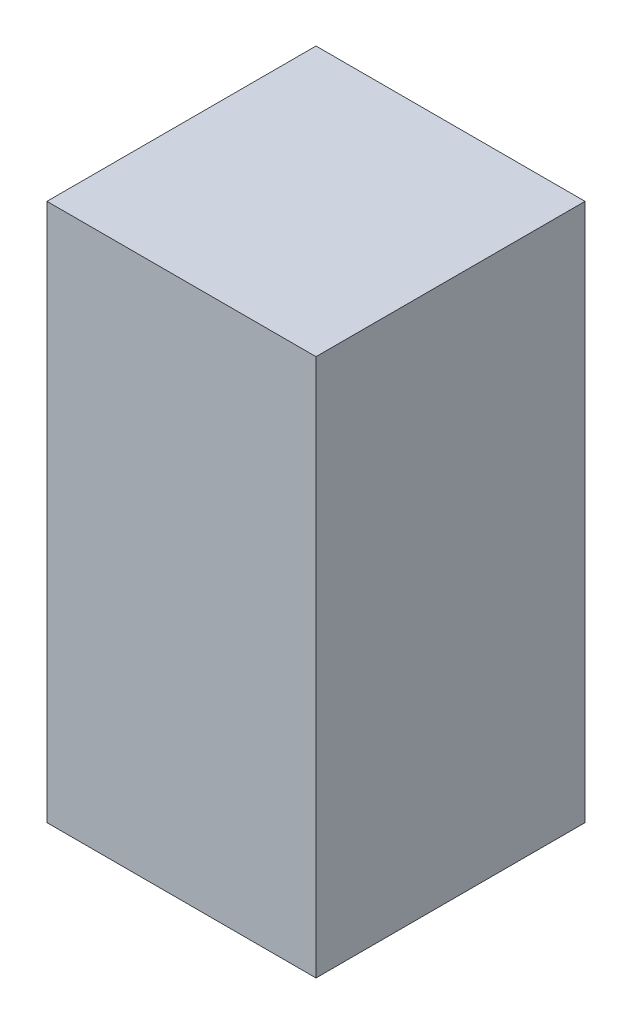
SolidWorks part; units mm, degrees
ref_plane "Front" through (0, 0, 0) normal (0, 0, 1) x (1, 0, 0)
ref_plane "Top" through (0, 0, 0) normal (0, 1, 0) x (1, 0, 0)
ref_plane "Right" through (0, 0, 0) normal (1, 0, 0) x (0, 0, -1)
sketch "Sketch1" plane through (0, 0, 0) normal (0, 1, 0) x (1, 0, 0)
  line L1 (0, 0) -> (200, 0)
  line L2 (0, 0) -> (0, -200)
  line L3 (0, -200) -> (200, -200)
  line L4 (200, 0) -> (200, -200)
  dimension "D1" = 200
  dimension "D2" = 200
extrude "Boss-Extrude1" add sketch "Sketch1" along normal blind 400
